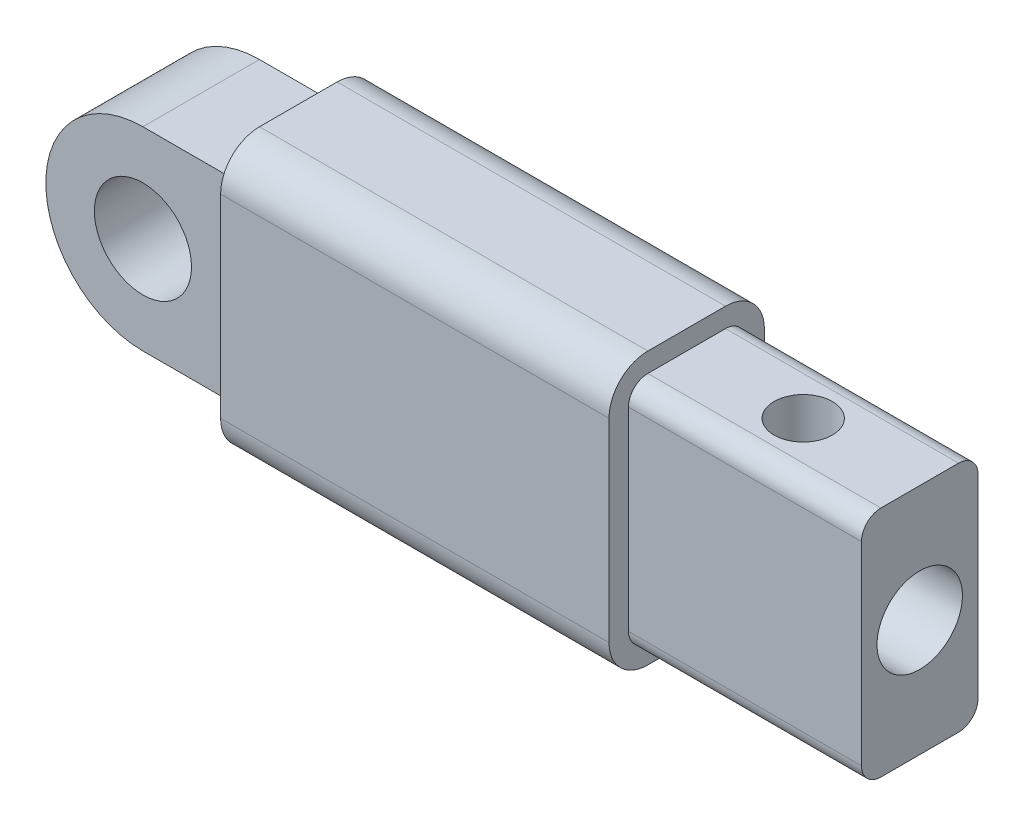
SolidWorks part; units mm, degrees
material "Thornel VCB-20 Carbon Cloth"
ref_plane "Front Plane" through (0, 0, 0) normal (0, 0, 1) x (1, 0, 0)
ref_plane "Top Plane" through (0, 0, 0) normal (0, 1, 0) x (1, 0, 0)
ref_plane "Right Plane" through (0, 0, 0) normal (1, 0, 0) x (0, 0, -1)
sketch "Sketch1" plane through (0, 0, 0) normal (0, 1, 0) x (1, 0, 0)
  line L0 (0, 0) -> (100, 0)
  dimension "D1" = 100
other "Structural Member1"
ref_plane "Plane1" through (0, 0, 0) normal (1, 0, 0) x (0, 0, -1)
sketch "Sketch11" plane through (0, 0, 0) normal (1, 0, 0) x (0, 0, -1)
  line L0 (-10, -30) -> (10, -30)
  line L1 (-15, -25) -> (-15, 25)
  line L2 (10, 30) -> (-10, 30)
  line L3 (15, 25) -> (15, -25)
  line L4 (-10, -35) -> (10, -35)
  line L5 (-20, -25) -> (-20, 25)
  line L6 (10, 35) -> (-10, 35)
  line L7 (20, 25) -> (20, -25)
  arc A0 (20, 25) -> (10, 35) centre (10, 25) ccw
  arc A1 (10, -35) -> (20, -25) centre (10, -25) ccw
  arc A2 (-20, -25) -> (-10, -35) centre (-10, -25) ccw
  arc A3 (-10, 35) -> (-20, 25) centre (-10, 25) ccw
  arc A4 (-10, 30) -> (-15, 25) centre (-10, 25) ccw
  arc A5 (15, 25) -> (10, 30) centre (10, 25) ccw
  arc A6 (10, -30) -> (15, -25) centre (10, -25) ccw
  arc A7 (-15, -25) -> (-10, -30) centre (-10, -25) ccw
  point P0 (0, 35)
  point P1 (20, 0)
  point P2 (0, -35)
  point P3 (-20, 0)
  point P4 (-20, 35)
  point P5 (20, 35)
  point P6 (20, -35)
  point P7 (-20, -35)
  point P8 (0, 0)
  point P33 (0, 0)
  dimension "D1" = 10
  dimension "Thickness" = 5
  dimension "V_leg" = 70
  dimension "H_leg" = 40
sketch "Sketch16" plane through (100, 0, 0) normal (1, 0, 0) x (0, 0, -1)
  line L0 (15, -25) -> (15, 25) construction
  line L1 (10, 30) -> (-10, 30) construction
  line L2 (-15, 25) -> (-15, -25) construction
  line L3 (-10, -30) -> (10, -30) construction
  line L4 (15, -25) -> (15, 25)
  line L5 (10, 30) -> (-10, 30)
  line L6 (-15, 25) -> (-15, -25)
  line L7 (-10, -30) -> (10, -30)
  arc A0 (15, 25) -> (10, 30) centre (10, 25) ccw construction
  arc A1 (-10, 30) -> (-15, 25) centre (-10, 25) ccw construction
  arc A2 (-15, -25) -> (-10, -30) centre (-10, -25) ccw construction
  arc A3 (10, -30) -> (15, -25) centre (10, -25) ccw construction
  arc A4 (15, 25) -> (10, 30) centre (10, 25) ccw
  arc A5 (-10, 30) -> (-15, 25) centre (-10, 25) ccw
  arc A6 (-15, -25) -> (-10, -30) centre (-10, -25) ccw
  arc A7 (10, -30) -> (15, -25) centre (10, -25) ccw
extrude "Boss-Extrude1" add sketch "Sketch16" along normal blind 60 and the other way blind 150 separate body
sketch "Sketch20" plane through (160, 0, 0) normal (1, 0, 0) x (0, 0, -1)
  circle A0 centre (0, 0) radius 11
  dimension "D1" = 22
extrude "Cut-Extrude6" cut sketch "Sketch20" against normal blind 30
sketch "Sketch21" plane through (0, 30, 0) normal (0, 1, 0) x (1, 0, 0)
  line L0 (100, 10) -> (100, -10) construction
  line L1 (-50, -10) -> (160, -10) construction
  line L2 (100, 10) -> (100, -10) construction
  line L3 (130, 10) -> (130, -10) construction
  circle A0 centre (130, 0) radius 7.5
  dimension "D1" = 15
extrude "Cut-Extrude7" cut sketch "Sketch21" against normal through all
sketch "Sketch22" plane through (0, 0, -15) normal (0, 0, -1) x (-1, 0, 0)
  line L0 (25, -25) -> (0, -25)
  line L1 (25, 25) -> (25, -25) construction
  line L2 (50, -25) -> (-160, -25) construction
  line L3 (0, -25) -> (0, -30)
  line L5 (50, -30) -> (-160, -30) construction
  line L7 (25, 25) -> (0, 25)
  line L8 (50, 25) -> (-160, 25) construction
  line L9 (0, -25) -> (0, 25) construction
  line L10 (0, 25) -> (0, 35)
  arc A0 (25, -25) -> (25, 25) centre (25, 0) ccw
extrude "Cut-Extrude11" cut sketch "Sketch22" against normal through all and the other way through all
sketch "Sketch23" plane through (0, 0, -15) normal (0, 0, -1) x (-1, 0, 0)
  circle A0 centre (25, 0) radius 12.5
  dimension "D1" = 25
extrude "Cut-Extrude12" cut sketch "Sketch23" against normal through all
